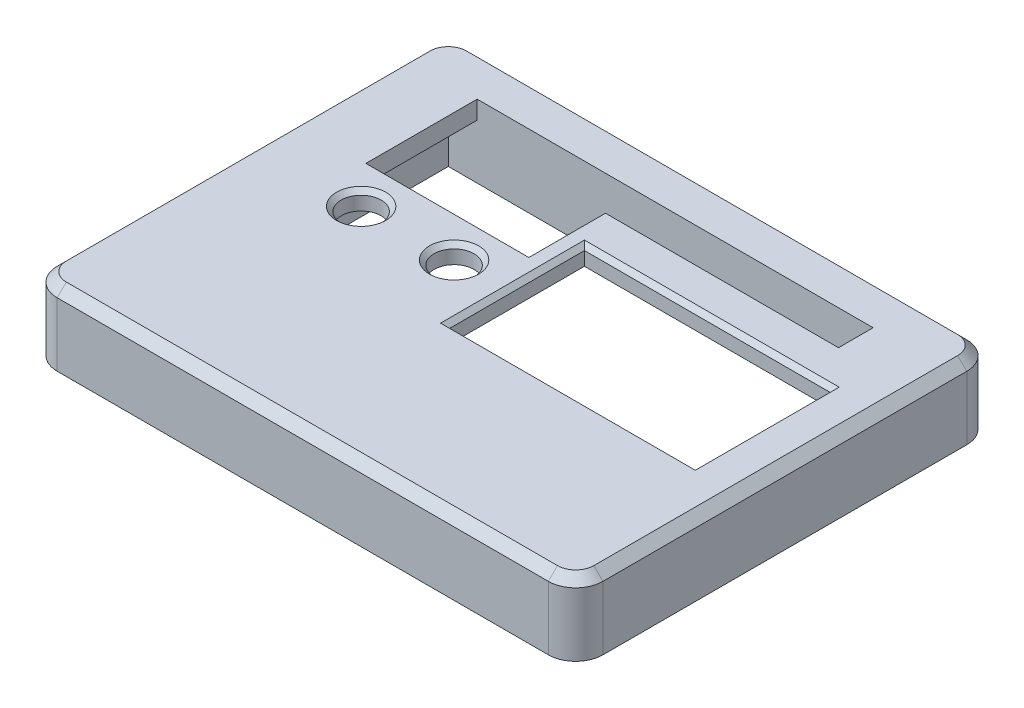
SolidWorks part; units mm, degrees
ref_plane "Front Plane" through (0, 0, 0) normal (0, 0, 1) x (1, 0, 0)
ref_plane "Top Plane" through (0, 0, 0) normal (0, 1, 0) x (1, 0, 0)
ref_plane "Right Plane" through (0, 0, 0) normal (1, 0, 0) x (0, 0, -1)
sketch "Sketch8" plane through (0, 0, 0) normal (0, 1, 0) x (1, 0, 0)
  line L0 (122.2624, 283.0831) -> (611.3122, 283.0831) construction
  line L3 (3.0219, 46.1944) -> (57.0219, 46.1944)
  line L6 (5.0219, 41.1944) -> (55.0219, 41.1944)
  line L7 (5.0219, 28.958) -> (5.0219, 5.1944)
  line L8 (5.0219, 5.1944) -> (55.0219, 5.1944)
  line L9 (55.0219, 37.388) -> (55.0219, 5.1944)
  line L10 (60.0219, 43.1944) -> (60.0219, 3.1944)
  line L11 (3.0219, 0.1944) -> (57.0219, 0.1944)
  line L12 (0.0219, 43.1944) -> (0.0219, 3.1944)
  line L13 (0.0219, 46.1944) -> (60.0219, 46.1944) construction
  line L14 (60.0219, 46.1944) -> (60.0219, 0.1944) construction
  line L15 (0.0219, 0.1944) -> (60.0219, 0.1944) construction
  line L16 (0.0219, 46.1944) -> (0.0219, 0.1944) construction
  line L17 (109.5, 253) -> (547.5, 253) construction
  line L18 (30.0219, 46.1944) -> (30.0219, 41.1944) construction
  line L19 (0.0219, 23.1944) -> (60.0219, 23.1944) construction
  line L20 (5.0219, 18.3508) -> (5.0219, 28.958)
  line L21 (55.0219, 5.1944) -> (5.0219, 5.1944)
  line L22 (55.0219, 5.1944) -> (55.0219, 18.3508)
  line L23 (55.0219, 18.3508) -> (28.0074, 18.3508)
  line L24 (5.0219, 5.1944) -> (5.0219, 18.3508)
  line L25 (26.1103, 28.958) -> (26.1103, 37.388)
  line L26 (5.0219, 28.958) -> (26.1103, 28.958)
  line L27 (26.1103, 37.388) -> (55.0219, 37.388)
  line L28 (5.0219, 41.1944) -> (5.0219, 5.1944) construction
  line L29 (28.0074, 20.6518) -> (28.0074, 18.3508)
  line L30 (8.1939, 41.1944) -> (8.1939, 28.958)
  line L31 (28.0074, 28.958) -> (28.0074, 20.6518)
  line L32 (55.0219, 37.388) -> (55.0219, 33.173)
  line L33 (55.0219, 33.173) -> (28.0074, 33.173)
  line L34 (28.0074, 33.173) -> (28.0074, 28.958)
  line L35 (55.0219, 37.388) -> (55.0219, 33.173)
  line L36 (51.7242, 37.388) -> (51.7242, 41.1944)
  line L38 (55.0219, 41.1944) -> (55.0219, 5.1944) construction
  arc A4 (57.0219, 46.1944) -> (60.0219, 43.1944) centre (57.0219, 43.1944) cw
  arc A5 (60.0219, 3.1944) -> (57.0219, 0.1944) centre (57.0219, 3.1944) cw
  arc A6 (3.0219, 0.1944) -> (0.0219, 3.1944) centre (3.0219, 3.1944) cw
  arc A7 (0.0219, 43.1944) -> (3.0219, 46.1944) centre (3.0219, 43.1944) cw
  circle A8 centre (30.0219, 43.6944) radius 1.6
  circle A9 centre (30.0219, 2.6944) radius 1.6
  circle A10 centre (2.5219, 23.1944) radius 1.6
  circle A11 centre (12.0219, 24.608) radius 2.2
  circle A12 centre (22.2402, 24.608) radius 2.2
  dimension "D3" = 5
  dimension "D4" = 3
  dimension "D6" = 2.5
  dimension "D7" = 3.2
  dimension "D5" = 3.2
  dimension "D8" = 4.4
  dimension "D9" = 4.4
  dimension "D1" = 36
  dimension "D2" = 50
  dimension "D10" = 7
extrude "Boss-Extrude4" add sketch "Sketch8" along normal blind 8 contours L34 L33 L9 L27 L25 L26 L7 L8 L23 L29 L31 A12 A11 | A7 L12 A6 L11 A5 L10 A4 L3 A10 L7 L20 L6 L9 L8 A8 A9
sketch "Sketch13" plane through (0, 8, 0) normal (0, 1, 0) x (1, 0, 0)
  circle A0 centre (2.5219, 23.1944) radius 1.6
  circle A1 centre (30.0219, 2.6944) radius 1.6
  circle A2 centre (30.0219, 43.6944) radius 1.6
extrude "Boss-Extrude5" add sketch "Sketch13" against normal blind 3
chamfer "Chamfer1" distance 1 angle 45 8 edges at (30.0219, 8, -46.1944) (59.1432, 8, -45.3157) (60.0219, 8, -23.1944) (59.1432, 8, -1.0731) (30.0219, 8, -0.1944) (0.9006, 8, -1.0731) (0.0219, 8, -23.1944) (0.9006, 8, -45.3157)
chamfer "Chamfer2" distance 0.5 angle 45 4 edges at (41.5146, 8, -18.3508) (55.0219, 8, -25.7619) (41.5146, 8, -33.173) (28.0074, 8, -25.7619)
chamfer "Chamfer3" distance 0.5 angle 45 2 edges at (22.2402, 8, -22.408) (12.0219, 8, -22.408)
sketch "Sketch14" plane through (0, 0, 0) normal (0, -1, 0) x (1, 0, 0)
  line L0 (55.0219, -33.173) -> (55.0219, -18.3508) construction
  line L1 (5.0219, -41.1944) -> (55.0219, -41.1944)
  line L2 (5.0219, -41.1944) -> (5.0219, -5.1944)
  line L3 (5.0219, -5.1944) -> (55.0219, -5.1944)
  line L4 (55.0219, -41.1944) -> (55.0219, -5.1944)
  dimension "D1" = 36
  dimension "D2" = 50
  dimension "D3" = 0
extrude "Cut-Extrude1" cut sketch "Sketch14" against normal blind 6
sketch "Sketch15" plane through (26.1103, 0, 0) normal (-1, 0, 0) x (0, 0, 1)
  line L0 (-37.388, 7) -> (-34.0867, 6)
  line L1 (-37.388, 8) -> (-37.388, 6) construction
  line L2 (-28.958, 6) -> (-37.388, 6) construction
  line L3 (-34.0867, 6) -> (-37.388, 6)
  line L4 (-37.388, 6) -> (-37.388, 7)
extrude "Cut-Extrude2" cut sketch "Sketch15" against normal blind 26 contours L0 L3 L4
